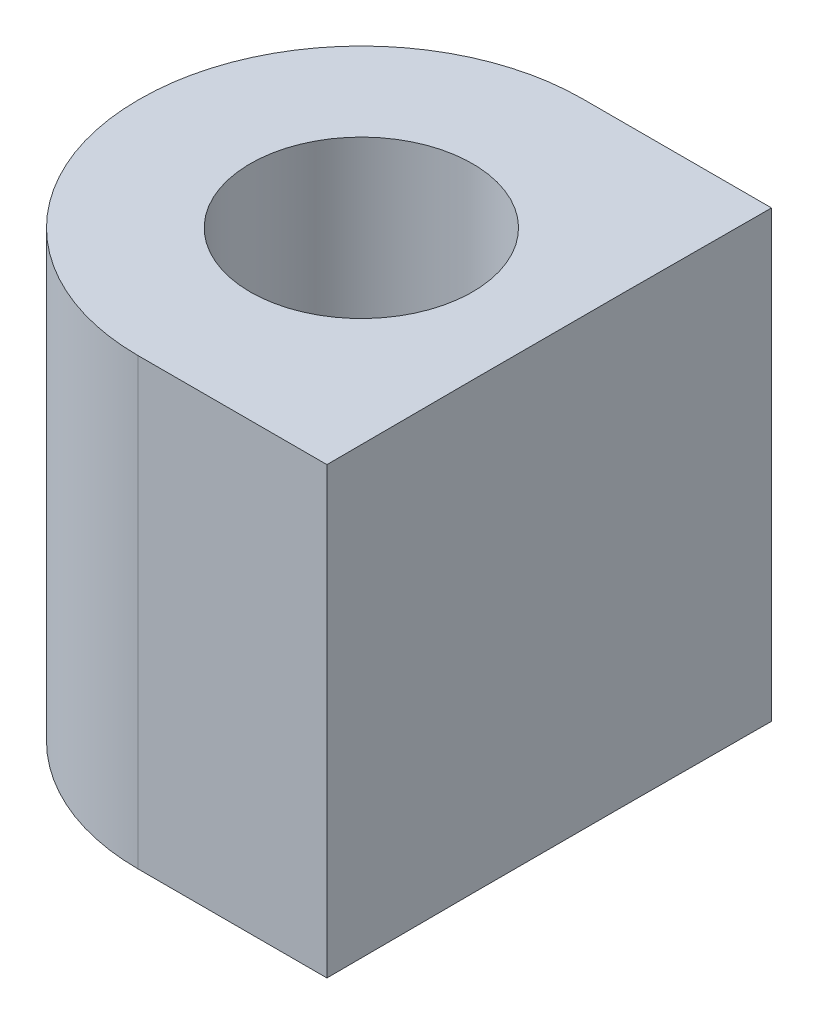
SolidWorks part; units mm, degrees
ref_plane "Front Plane" through (0, 0, 0) normal (0, 0, 1) x (1, 0, 0)
ref_plane "Top Plane" through (0, 0, 0) normal (0, 1, 0) x (1, 0, 0)
ref_plane "Right Plane" through (0, 0, 0) normal (1, 0, 0) x (0, 0, -1)
sketch "Sketch1" plane through (0, 0, 0) normal (0, 1, 0) x (1, 0, 0)
  line L1 (-0.0254, -6.35) -> (5.3661, -6.35)
  line L2 (-6.35, -0.0254) -> (-6.35, 0.0254)
  line L3 (-0.0254, 6.35) -> (5.3661, 6.35)
  line L4 (6.35, -6.35) -> (6.35, 6.35) construction
  line L5 (-6.35, -6.35) -> (6.35, 6.35) construction
  line L6 (-6.35, 6.35) -> (6.35, -6.35) construction
  circle A0 centre (0, 0) radius 3.175
  arc A1 (-6.35, -0.0254) -> (-0.0254, -6.35) centre (-0.0254, -0.0254) ccw
  arc A2 (-0.0254, 6.35) -> (-6.35, 0.0254) centre (-0.0254, 0.0254) ccw
  arc A3 (5.3661, 6.35) -> (5.3661, -6.35) centre (1255.35, 0) ccw
  point P0 (0, 0)
  dimension "D3" = 6.35
  dimension "D4" = 6.3246
  dimension "D6" = 2500
  dimension "D1" = 12.7
  dimension "D2" = 12.7
  dimension "D5" = 1249
extrude "Boss-Extrude1" add sketch "Sketch1" along normal blind 12.7
